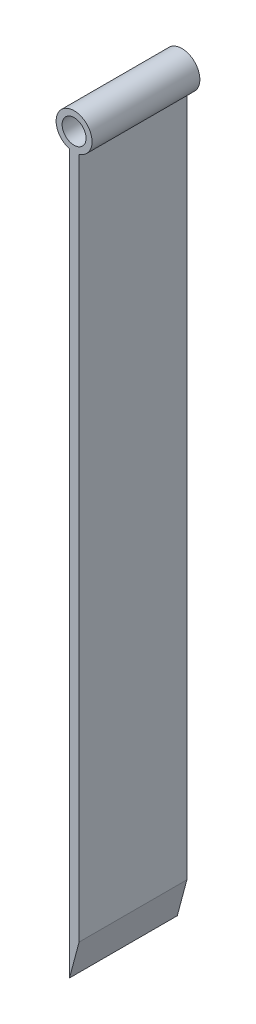
SolidWorks part; units mm, degrees
ref_plane "Alzado" through (0, 0, 0) normal (0, 0, 1) x (1, 0, 0)
ref_plane "Planta" through (0, 0, 0) normal (0, 1, 0) x (1, 0, 0)
ref_plane "Vista lateral" through (0, 0, 0) normal (1, 0, 0) x (0, 0, -1)
sketch "Croquis1" plane through (0, 0, 0) normal (0, 0, 1) x (1, 0, 0)
  line L0 (0, 149.8744) -> (0, 0)
  line L1 (0, 0) -> (2, 7.5)
  line L2 (2, 7.5) -> (2, 149.8977)
  circle A0 centre (0.9579, 153.5) radius 3.75
  circle A1 centre (0.9579, 153.5) radius 2.5
  dimension "D4" = 5
  dimension "D5" = 7.5
extrude "Saliente-Extruir1" add sketch "Croquis1" along normal blind 22.5 contours A0 A1 | A0 L0 L1 L2
